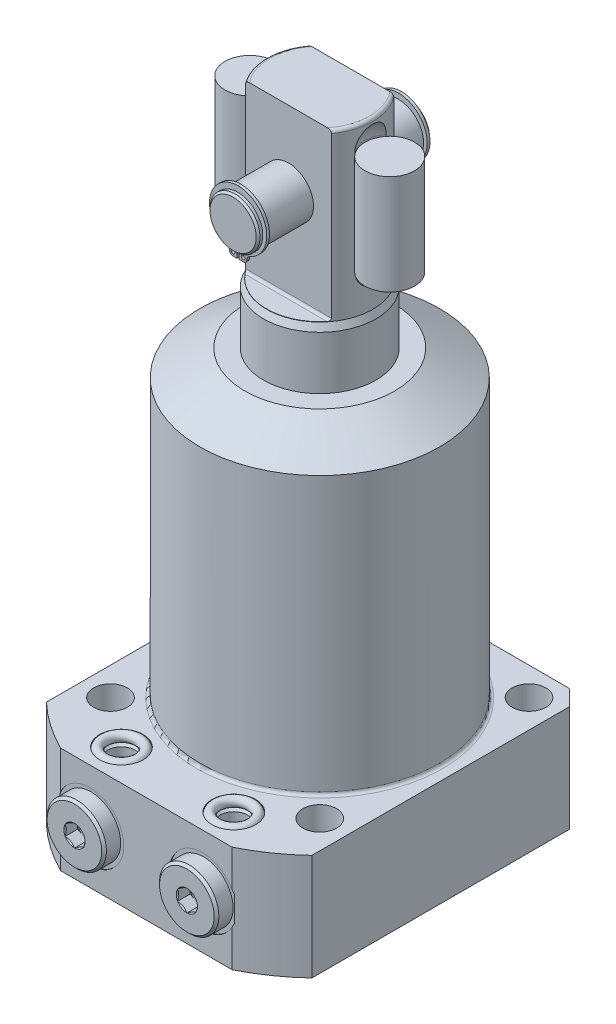
SolidWorks part; units mm, degrees
material "AISI 1020"
ref_plane "Front Plane" through (0, 0, 0) normal (0, 0, 1) x (1, 0, 0)
ref_plane "Top Plane" through (0, 0, 0) normal (0, 1, 0) x (1, 0, 0)
ref_plane "Right Plane" through (0, 0, 0) normal (1, 0, 0) x (0, 0, -1)
sketch "Sketch1" plane through (0, 0, 0) normal (0, 0, 1) x (1, 0, 0)
  line L0 (18, 0) -> (18, 114)
  line L1 (18, 114) -> (17, 116.1445)
  line L2 (17, 116.1445) -> (17, 168.25)
  line L3 (16, 169.25) -> (0, 169.25)
  line L4 (0, 61.9815) -> (0, 93.5758) construction
  line L8 (0, -3.075) -> (0, 64.575) construction
  line L9 (18, 0) -> (0, 0)
  line L10 (0, 0) -> (0, 169.25)
  line L11 (-25.0821, -34) -> (21.8096, -34) construction
  arc A0 (17, 168.25) -> (16, 169.25) centre (16, 168.25) ccw
  dimension "D1" = 1
  dimension "D2" = 36
  dimension "D3" = 34
  dimension "D4" = 55.25
  dimension "D5" = 34
  dimension "D6" = 25
  dimension "D7" = 203.25
revolve "PLUNGER" add sketch "Sketch1" angle 360 about L8
ref_plane "FLAT_SKTCH_PLN" through (0, 0, 0) normal (1, 0, 0) x (0, 0, -1)
sketch "Sketch17" plane through (0, 0, 0) normal (1, 0, 0) x (0, 0, -1)
  line L0 (16, 169.25) -> (-16, 169.25) construction
  line L1 (17, 116.1445) -> (17, 168.25) construction
  line L2 (16, 169.25) -> (-16, 169.25)
  line L3 (17, 116.1445) -> (17, 168.25)
  line L5 (10, 169.25) -> (17, 169.25)
  line L6 (10, 169.25) -> (10, 117.05)
  line L7 (10.8, 116.25) -> (17, 116.25)
  line L8 (17, 169.25) -> (17, 116.25)
  line L9 (0, 168.25) -> (0, 116.1445) construction
  line L10 (0, 57.0947) -> (0, 92.2162) construction
  line L11 (0, 114) -> (0, 0) construction
  line L12 (0, 114) -> (0, 116.1445) construction
  line L13 (-17, 169.25) -> (-17, 116.25)
  line L14 (-10.8, 116.25) -> (-17, 116.25)
  line L15 (-10, 169.25) -> (-10, 117.05)
  line L16 (-10, 169.25) -> (-17, 169.25)
  line L17 (-17, 116.1445) -> (-17, 168.25)
  arc A0 (10, 117.05) -> (10.8, 116.25) centre (10.8, 117.05) ccw
  arc A1 (-10, 117.05) -> (-10.8, 116.25) centre (-10.8, 117.05) cw
  dimension "D3" = 0.8
  dimension "D1" = 53
  dimension "D2" = 20
extrude "FLATS" cut sketch "Sketch17" against normal mid plane 100 contours L6 A0 L7 L8 L5 | L13 L14 A1 L15 L16
sketch "Sketch22" plane through (0, 0, 0) normal (1, 0, 0) x (0, 0, -1)
  line L0 (-11.5689, 145.25) -> (12.3381, 145.25) construction
  line L1 (0, 87.9433) -> (0, 65.5754) construction
  line L2 (0, 172.8601) -> (0, 160.5297) construction
  line L3 (0, 168.25) -> (0, 116.1445) construction
  line L4 (10, 169.25) -> (-10, 169.25) construction
  line L5 (10, 169.25) -> (-10, 169.25)
  line L6 (27.75, 152.65) -> (27.15, 153.25)
  line L7 (27.15, 153.25) -> (26.25, 153.25)
  line L8 (27.75, 152.65) -> (27.75, 145.25)
  line L9 (27.75, 145.25) -> (-27.75, 145.25)
  line L11 (26.25, 153.25) -> (26.25, 152.7175)
  line L12 (26.25, 152.7175) -> (25.25, 152.7175)
  line L13 (25.25, 152.7175) -> (25.25, 153.25)
  line L14 (25.25, 153.25) -> (-25.25, 153.25)
  line L15 (-25.25, 152.7175) -> (-25.25, 153.25)
  line L16 (-26.25, 152.7175) -> (-25.25, 152.7175)
  line L17 (-26.25, 153.25) -> (-26.25, 152.7175)
  line L18 (-27.75, 152.65) -> (-27.75, 145.25)
  line L19 (-27.15, 153.25) -> (-26.25, 153.25)
  line L20 (-27.75, 152.65) -> (-27.15, 153.25)
  dimension "D1" = 24
  dimension "D2" = 45
  dimension "D3" = 0.6
  dimension "D4" = 16
  dimension "D5" = 1
  dimension "D6" = 14.935
  dimension "D7" = 55.5
  dimension "D8" = 50.5
revolve "PIVOT_PIN" add sketch "Sketch22" angle 360 about L0
sketch "Sketch23" plane through (0, 0, -25.25) normal (0, 0, -1) x (-1, 0, 0)
  line L0 (0, 79.466) -> (0, 70.8639) construction
  line L1 (0, 168.25) -> (0, 116.1445) construction
  line L2 (0, 145.25) -> (-4.1358, 135.8979) construction
  line L3 (-0.35, 134.7079) -> (-1.61, 134.7079)
  line L4 (0, 145.25) -> (4.1358, 135.8979) construction
  line L5 (0.35, 137.5079) -> (0.35, 134.7079)
  line L6 (-0.35, 137.5079) -> (-0.35, 134.7079)
  line L7 (0.35, 134.7079) -> (1.61, 134.7079)
  arc A0 (0.35, 137.5079) -> (-0.35, 137.5079) centre (0, 145.25) ccw
  arc A1 (-2.8, 135.8979) -> (-1.61, 134.7079) centre (-1.61, 135.8979) ccw
  arc A2 (-2.8, 135.8979) -> (-3.5955, 137.1195) centre (-4.1358, 135.8979) ccw
  arc A3 (-3.5955, 137.1195) -> (0, 155.03) centre (0.1884, 145.676) cw
  circle A4 centre (-1.61, 135.8979) radius 0.595
  circle A5 centre (1.61, 135.8979) radius 0.595
  arc A6 (3.5955, 137.1195) -> (0, 155.03) centre (-0.1884, 145.676) ccw
  arc A7 (2.8, 135.8979) -> (3.5955, 137.1195) centre (4.1358, 135.8979) cw
  arc A8 (2.8, 135.8979) -> (1.61, 134.7079) centre (1.61, 135.8979) cw
  point P17 (-3.1344, 138.1621)
  point P27 (3.1344, 138.1621)
  point P28 (0, 153)
  dimension "D1" = 15.5
  dimension "D3" = 1.19
  dimension "D8" = 1.19
  dimension "D2" = 0.7
  dimension "D4" = 2.8
  dimension "D5" = 2.8
  dimension "D6" = 2.03
  dimension "D7" = 1.14
extrude "RETAINING_RING" add sketch "Sketch23" along normal blind 0.89
ref_plane "PIN_CL" through (0, 0, 0) normal (0, 0, 1) x (1, 0, 0)
mirror "RETAINING_RING-OPP" about plane through (0, 0, 0) normal (0, 0, 1) of "RETAINING_RING"
sketch "Sketch20" plane through (0, 0, 0) normal (0, 0, 1) x (1, 0, 0)
  line L0 (-12.49, 169.25) -> (12.49, 169.25) construction
  line L1 (-12.49, 169.25) -> (12.49, 169.25)
  line L2 (0, 87.5232) -> (0, 65.9324) construction
  line L3 (0, 172.858) -> (0, 160.534) construction
  line L4 (0, 168.25) -> (0, 116.1445) construction
  line L5 (22.4375, 82.048) -> (22.4375, 54.8595) construction
  line L6 (14.5, 161.75) -> (14.5, 128.75)
  line L7 (22.4375, 169.6875) -> (22.4375, 120.8125)
  arc A0 (22.4375, 169.6875) -> (14.5, 161.75) centre (22.4375, 161.75) ccw
  arc A1 (14.5, 128.75) -> (22.4375, 120.8125) centre (22.4375, 128.75) ccw
  dimension "D3" = 33
  dimension "D1" = 14.5
  dimension "D2" = 15.875
  dimension "D4" = 7.5
revolve "SPRING_SLOT" cut sketch "Sketch20" angle 360 about L5
mirror "SPRING_SLOT_OPP" about plane through (0, 0, 0) normal (1, 0, 0) of "SPRING_SLOT"
sketch "Sketch24" plane through (0, 0, 0) normal (0, 0, 1) x (1, 0, 0)
  line L0 (7.2759, 145.25) -> (-10.8708, 145.25) construction
  line L1 (-22.4075, 84.5678) -> (-22.4075, 68.6953) construction
  line L2 (-14.5, 128.75) -> (-14.5, 161.75) construction
  line L3 (-14.47, 161.25) -> (-22.4075, 161.25)
  line L4 (-14.47, 161.25) -> (-14.47, 129.25)
  line L6 (-22.4075, 161.25) -> (-22.4075, 129.25)
  line L7 (-14.47, 129.25) -> (-22.4075, 129.25)
  dimension "D1" = 15.875
  dimension "D2" = 32
  dimension "D3" = 0.03
revolve "SPRING" add sketch "Sketch24" angle 360 about L1
mirror "SPRING_OPP" about plane through (0, 0, 0) normal (1, 0, 0) of "SPRING"
sketch "Sketch6" plane through (0, 0, 0) normal (0, 0, 1) x (1, 0, 0)
  line L0 (0, -34) -> (0, 67.6291) construction
  line L1 (0, 97) -> (24, 97)
  line L2 (24, 97) -> (38.385, 88.6948)
  line L3 (61.915, 0) -> (61.915, -34)
  line L4 (0, -34) -> (61.915, -34)
  line L5 (38.385, 0) -> (38.385, 88.6948)
  line L6 (61.915, 0) -> (38.385, 0)
  line L7 (0, -34) -> (0, 97)
  dimension "D1" = 76.77
  dimension "D2" = 34
  dimension "D3" = 131
  dimension "D4" = 123.83
  dimension "D5" = 30
  dimension "D6" = 48
revolve "BODY_REVOLVE" add sketch "Sketch6" angle 360 about L0
sketch "Sketch7" plane through (0, 0, 0) normal (0, 1, 0) x (-1, 0, 0)
  line L0 (0, 0) -> (0, -52.3237) construction
  line L1 (-42.5, 55.5) -> (42.5, 55.5)
  line L2 (-42.5, 55.5) -> (-42.5, -42.5)
  line L3 (-42.5, -42.5) -> (42.5, -42.5)
  line L4 (42.5, 55.5) -> (42.5, -42.5)
  dimension "D1" = 85
  dimension "D2" = 98
  dimension "D3" = 42.5
extrude "FLANGE_SIDES" cut sketch "Sketch7" against normal through all flip side to cut
sketch "Sketch8" plane through (0, -34, 0) normal (0, -1, 0) x (1, 0, 0)
  circle A0 centre (-33.5, 33.5) radius 5.4
  dimension "D1" = 10.8
  dimension "D2" = 33.5
  dimension "D3" = 33.5
extrude "MOUNTING HOLES" cut sketch "Sketch8" against normal through all
pattern_circular "MOUNTING_PATTERN" count 4 over 360 about axis through (0, 0, 0) along (0, 1, 0) of "MOUNTING HOLES"
chamfer "FLANGE_CHAMFER" distance 5 angle 45 2 edges at (-42.5, -17, -42.5) (42.5, -17, -42.5)
fillet "BODY_FILLET" radius 1 1 edges at (38.385, 0, 0)
ref_plane "FLANGE-PORT_PLANE" through (0, -17, 0) normal (0, -1, 0) x (1, 0, 0)
sketch "Sketch11" plane through (0, -17, 0) normal (0, -1, 0) x (1, 0, 0)
  line L0 (-18, 42.9716) -> (-18, 19.7499) construction
  line L1 (-28.75, 55.5) -> (-28.75, 55.25)
  line L3 (-28.75, 55.25) -> (-24.65, 55.25)
  line L4 (-24.65, 55.25) -> (-23.945, 54.545)
  line L5 (-23.945, 54.545) -> (-23.945, 36.53)
  line L6 (-23.945, 36.53) -> (-18, 36.53)
  line L7 (-18, 36.53) -> (-18, 55.5)
  line L8 (-18, 55.5) -> (-28.75, 55.5)
  line L10 (27.4448, 55.5) -> (-27.4448, 55.5) construction
  dimension "D1" = 18
  dimension "D2" = 0.25
  dimension "D3" = 11.89
  dimension "D4" = 18.72
  dimension "D5" = 21.5
  dimension "D6" = 45
  dimension "D7" = 0.705
revolve "PORT SPOT FACE" cut sketch "Sketch11" angle 360 about L0
ref_plane "MANIFOLD_PORT_PLANE" through (0, 0, 45.5) normal (0, 0, 1) x (1, 0, 0)
sketch "Sketch13" plane through (0, 0, 45.5) normal (0, 0, 1) x (1, 0, 0)
  line L0 (-22.375, -22) -> (-22.375, -31)
  line L1 (-22.375, -31) -> (-23.125, -31.75)
  line L2 (-23.125, -31.75) -> (-25, -31.75)
  line L3 (-25, -31.75) -> (-25, -34)
  line L5 (-25, -34) -> (-18, -34)
  line L6 (-18, -34) -> (-18, -22)
  line L7 (-18, -22) -> (-22.375, -22)
  line L8 (-18, 15.2099) -> (-18, -4.3918) construction
  line L10 (27.4448, -34) -> (-27.4448, -34) construction
  dimension "D1" = 18
  dimension "D2" = 8.75
  dimension "D3" = 12
  dimension "D4" = 2.25
  dimension "D5" = 14
  dimension "D6" = 45
  dimension "D7" = 0.75
revolve "BOTTOM_MANIFOLD_PORT" cut sketch "Sketch13" angle 360 about L8
sketch "Sketch14" plane through (0, -17, 0) normal (0, -1, 0) x (1, 0, 0)
  line L0 (-18, 32.5881) -> (-18, 43.5576) construction
  line L1 (-18, 36.53) -> (-18, 54.545) construction
  line L2 (-21.4, 60.55) -> (-26.75, 60.55)
  line L3 (-26.75, 60.55) -> (-27.5, 59.8)
  line L4 (-27.5, 59.8) -> (-27.5, 55.25)
  line L5 (-7.25, 55.25) -> (-27.9447, 55.25) construction
  line L6 (-27.5, 55.25) -> (-22.125, 55.25)
  line L7 (-11.35, 55.25) -> (-24.65, 55.25) construction
  line L8 (-22.125, 55.25) -> (-22.125, 52.7472)
  line L9 (-22.125, 52.7472) -> (-18, 52.7472)
  line L10 (-18, 52.7472) -> (-18, 52.7482)
  line L11 (-18, 52.7482) -> (-21, 54.5508)
  line L12 (-21, 54.5508) -> (-21, 60.15)
  line L13 (-21, 60.15) -> (-21.4, 60.55)
  dimension "D1" = 8.25
  dimension "D2" = 2.5028
  dimension "D3" = 59
  dimension "D4" = 6
  dimension "D5" = 5.3
  dimension "D6" = 19
  dimension "D7" = 45
  dimension "D8" = 0.75
  dimension "D9" = 45
  dimension "D10" = 0.4
  dimension "D11" = 0.001
revolve "BSPP_PLUGHEAD" add sketch "Sketch14" angle 360 about L0
sketch "Sketch15" plane through (0, 0, 60.55) normal (0, 0, 1) x (1, 0, 0)
  line L1 (-15, -18.7321) -> (-15, -15.2679)
  line L2 (-15, -15.2679) -> (-18, -13.5359)
  line L3 (-18, -13.5359) -> (-21, -15.2679)
  line L4 (-21, -15.2679) -> (-21, -18.7321)
  line L5 (-21, -18.7321) -> (-18, -20.4641)
  line L6 (-18, -20.4641) -> (-15, -18.7321)
  circle A0 centre (-18, -17) radius 3 construction
  dimension "D1" = 6
extrude "BSPP_PLUG_HEX" cut sketch "Sketch15" against normal blind 4.06
mirror "MANIFOLD_TOP_MIRROR" about plane through (0, -17, 0) normal (0, -1, 0) of "BOTTOM_MANIFOLD_PORT"
mirror "BSPP-MANIFOLD_MIRROR" about plane through (0, 0, 0) normal (1, 0, 0) of "MANIFOLD_TOP_MIRROR", "PORT SPOT FACE", "BOTTOM_MANIFOLD_PORT", "BSPP_PLUGHEAD", "BSPP_PLUG_HEX"
sketch "Sketch16" plane through (0, 0, 45.5) normal (0, 0, 1) x (1, 0, 0)
  line L1 (-18, 9.3219) -> (-18, -15.1063) construction
  line L2 (-18, -31) -> (-18, -22) construction
  line L3 (27.4448, -34) -> (-27.4448, -34) construction
  circle A0 centre (-23.5, -33.25) radius 1.5
  dimension "D1" = 3
  dimension "D3" = 0.75
  dimension "D2" = 11
revolve "MANIFOLD_O-RING" add sketch "Sketch16" angle 360 about L1
mirror "MANIFOLD_O-RING_MIRROR" about plane through (0, 0, 0) normal (1, 0, 0) of bodies 128
mirror "MANIFOLD_O-RING_MIRROR_TOP" about plane through (0, -17, 0) normal (0, -1, 0) of bodies 128 130
